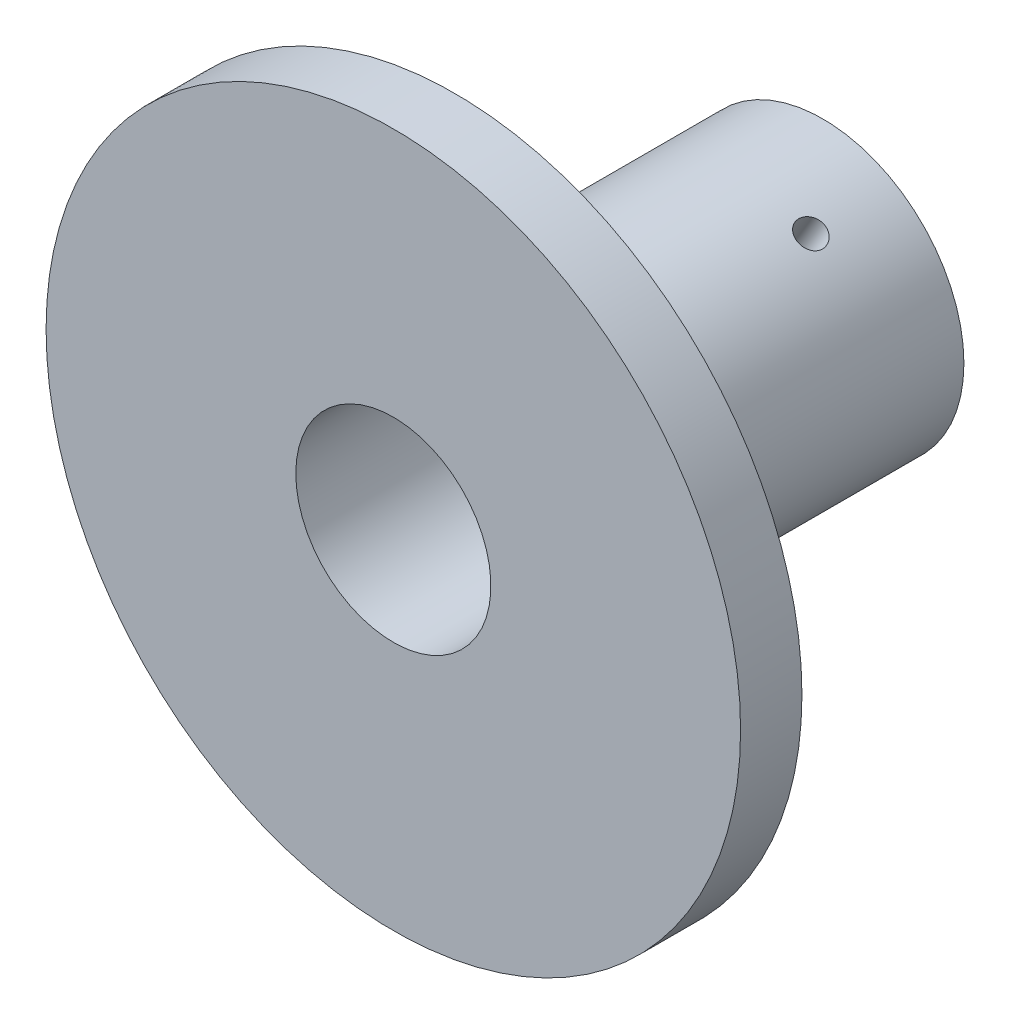
SolidWorks part; units mm, degrees
ref_plane "Front Plane" through (0, 0, 0) normal (0, 0, 1) x (1, 0, 0)
ref_plane "Top Plane" through (0, 0, 0) normal (0, 1, 0) x (1, 0, 0)
ref_plane "Right Plane" through (0, 0, 0) normal (1, 0, 0) x (0, 0, -1)
sketch "Sketch1" plane through (0, 0, 0) normal (0, 0, 1) x (1, 0, 0)
  circle A0 centre (0, 0) radius 28.3
  dimension "D1" = 56.6
extrude "Boss-Extrude1" add sketch "Sketch1" along normal blind 5
sketch "Sketch4" plane through (0, 0, 0) normal (0, 0, -1) x (-1, 0, 0)
  circle A0 centre (0, 0) radius 11.5
  dimension "D1" = 23
extrude "Boss-Extrude2" add sketch "Sketch4" along normal blind 30
sketch "Sketch10" plane through (0, 0, -30) normal (0, 0, -1) x (-1, 0, 0)
  circle A0 centre (0, 0) radius 7.95
  dimension "D1" = 15.9
extrude "Cut-Extrude4" cut sketch "Sketch10" against normal through all
hole_wizard "#4-40 Tapped Hole2" positions "3DSketch2" profile "Sketch11" tap size "#4-40" standard "Ansi Inch"
sketch3d "3DSketch2"
  point P0 (-11.4977, 0.2295, -23.0909)
sketch "Sketch11" plane through (-11.4977, 0.2295, -23.0909) normal (0, 0, 1) x (-0.02, -0.9998, 0)
  line L0 (0, 0) -> (0, 23)
  line L1 (0, 23) -> (1.1303, 23)
  line L2 (1.1303, 23) -> (1.1303, 0)
  line L5 (1.1303, 0) -> (0, 0)
  line L11 (0, -6.35) -> (0, 107.95) construction
  dimension "Thread Major Dia." = 2.2606
  dimension "Thru Tap Drill Depth" = 23
pattern_circular "CirPattern3" count 3 every 120 about axis through (0, 0, -30) along (0, 0, 1) of "#4-40 Tapped Hole2"
